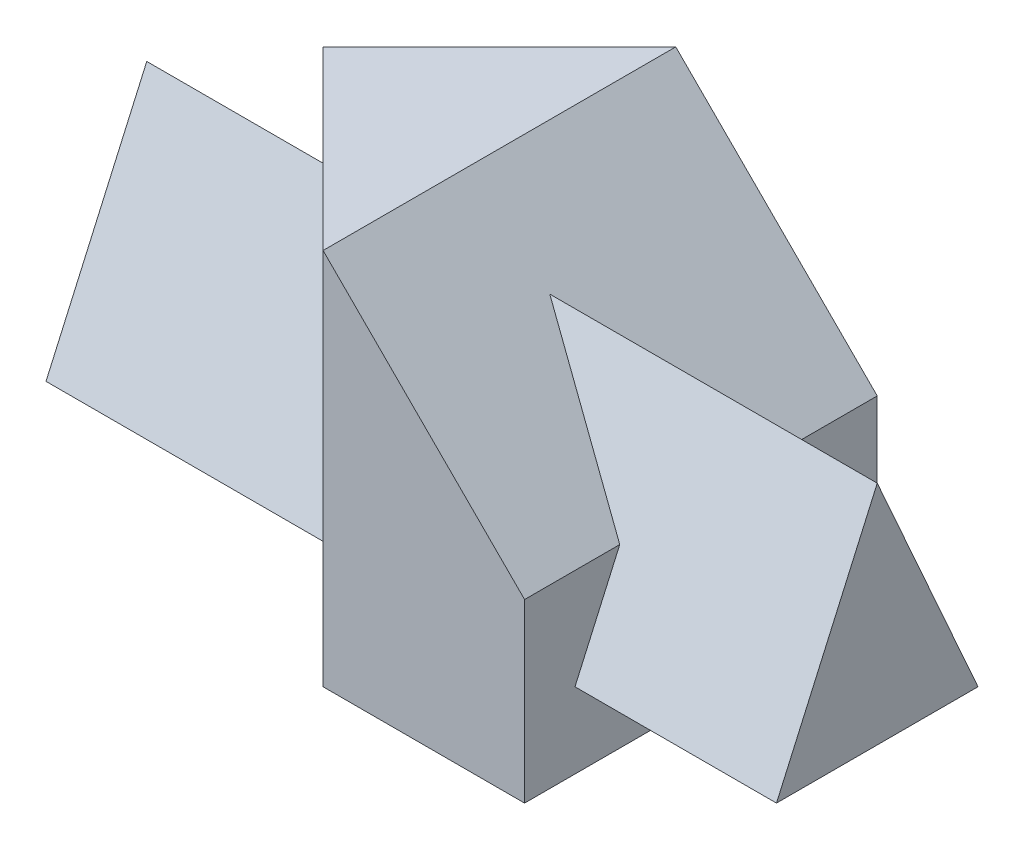
SolidWorks part; units mm, degrees
ref_plane "Front" through (0, 0, 0) normal (0, 0, 1) x (1, 0, 0)
ref_plane "Top" through (0, 0, 0) normal (0, 1, 0) x (1, 0, 0)
ref_plane "Right" through (0, 0, 0) normal (1, 0, 0) x (0, 0, -1)
sketch "Sketch1" plane through (0, 0, 0) normal (0, 1, 0) x (1, 0, 0)
  line L0 (0, 0) -> (35, 35)
  line L1 (35, 35) -> (75, 35)
  line L2 (75, 35) -> (75, -35)
  line L3 (75, -35) -> (35, -35)
  line L4 (35, -35) -> (0, 0)
  dimension "D1" = 35
  dimension "D2" = 70
  dimension "D3" = 40
  dimension "D4" = 40
extrude "Extrude1" add sketch "Sketch1" along normal blind 75
sketch "Sketch2" plane through (0, 0, 35) normal (0, 0, 1) x (1, 0, 0)
  line L0 (35, 75) -> (75, 35)
  line L1 (75, 75) -> (75, 0) construction
  line L2 (75, 35) -> (75, 75)
  line L3 (75, 75) -> (35, 75)
  line L4 (35, 0) -> (75, 0) construction
  dimension "D1" = 35
extrude "Cut-Extrude1" cut sketch "Sketch2" against normal through all
sketch "Sketch3" plane through (75, 0, 0) normal (1, 0, 0) x (0, 0, -1)
  line L0 (-25, 15) -> (15, 15)
  line L1 (15, 15) -> (-5, 60)
  line L2 (-5, 60) -> (-25, 15)
  line L3 (-35, 0) -> (35, 0) construction
  line L4 (35, 35) -> (35, 0) construction
  line L5 (35, 75) -> (-35, 75) construction
  dimension "D1" = 15
  dimension "D2" = 40
  dimension "D3" = 20
  dimension "D4" = 15
extrude "Extrude2" add sketch "Sketch3" along normal blind 40 and the other way blind 105
